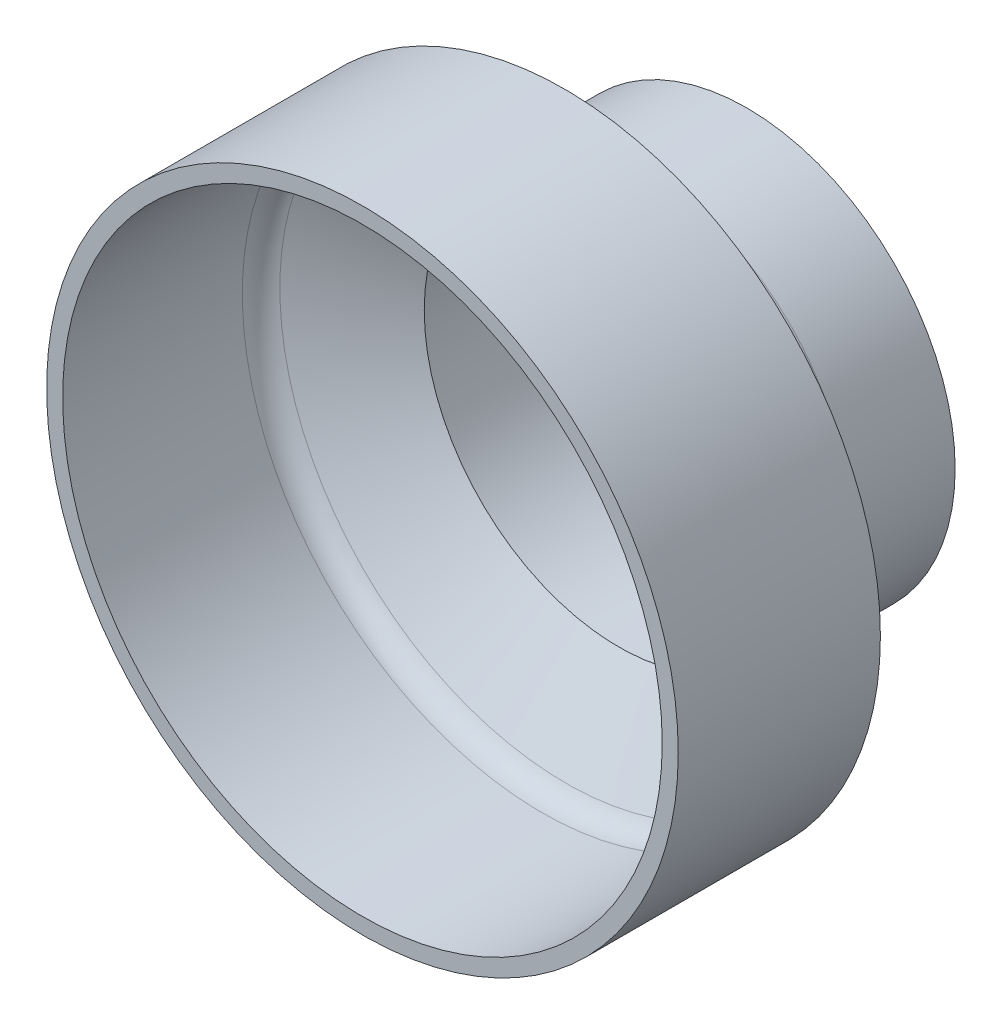
SolidWorks part; units mm, degrees
material "Alloy Steel"
ref_plane "Front Plane" through (0, 0, 0) normal (0, 0, 1) x (1, 0, 0)
ref_plane "Top Plane" through (0, 0, 0) normal (0, 1, 0) x (1, 0, 0)
ref_plane "Right Plane" through (0, 0, 0) normal (1, 0, 0) x (0, 0, -1)
sketch "Sketch1" plane through (0, 0, 0) normal (0, 1, 0) x (1, 0, 0)
  line L0 (6.35, -0.762) -> (10.795, -0.762)
  line L1 (10.795, -0.762) -> (10.795, -7.112)
  line L2 (10.795, -7.112) -> (15.875, -10.0449)
  line L3 (16.637, -11.3648) -> (16.637, -21.336)
  line L4 (16.637, -21.336) -> (17.526, -21.336)
  line L5 (17.526, -21.336) -> (17.526, -10.1183)
  line L6 (17.526, -10.1183) -> (12.319, -7.112)
  line L7 (11.557, -5.7922) -> (11.557, 0)
  line L8 (11.557, 0) -> (6.35, 0)
  line L9 (6.35, 0) -> (6.35, -0.762)
  line L10 (0, 0) -> (0, -21.336) construction
  arc A0 (15.875, -10.0449) -> (16.637, -11.3648) centre (15.113, -11.3648) cw
  arc A1 (12.319, -7.112) -> (11.557, -5.7922) centre (13.081, -5.7922) cw
revolve "Revolve1" add sketch "Sketch1" angle 360 about L10
